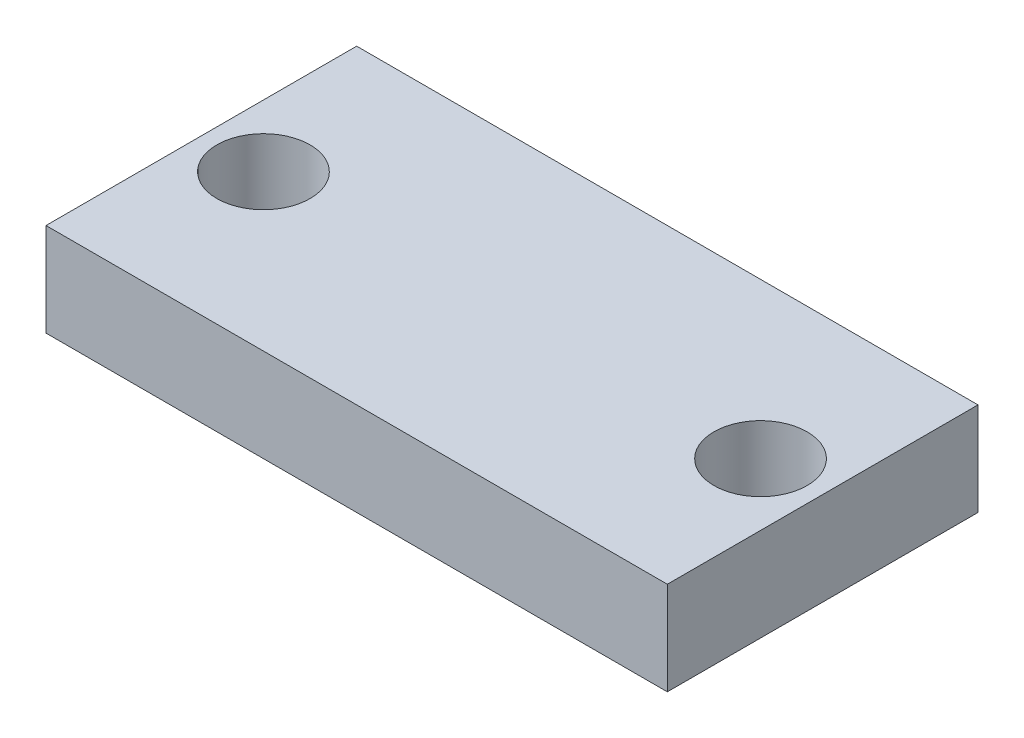
SolidWorks part; units mm, degrees
ref_plane "前视基准面" through (0, 0, 0) normal (0, 0, 1) x (1, 0, 0)
ref_plane "上视基准面" through (0, 0, 0) normal (0, 1, 0) x (1, 0, 0)
ref_plane "右视基准面" through (0, 0, 0) normal (1, 0, 0) x (0, 0, -1)
sketch "草图1" plane through (0, 0, 0) normal (0, 1, 0) x (1, 0, 0)
  line L0 (0, 0) -> (0, 5.2869)
  line L1 (0, 5.2869) -> (-20, 5.2869)
  line L2 (-20, 5.2869) -> (-20, -4.7131)
  line L3 (-20, -4.7131) -> (0, -4.7131)
  line L4 (0, -4.7131) -> (0, 0)
  circle A0 centre (-18, 0.2869) radius 1.5
  circle A1 centre (-2, 0.2869) radius 1.5
  dimension "D3" = 3
  dimension "D1" = 10
  dimension "D2" = 20
  dimension "D4" = 2
extrude "凸台-拉伸1" add sketch "草图1" along normal blind 3
